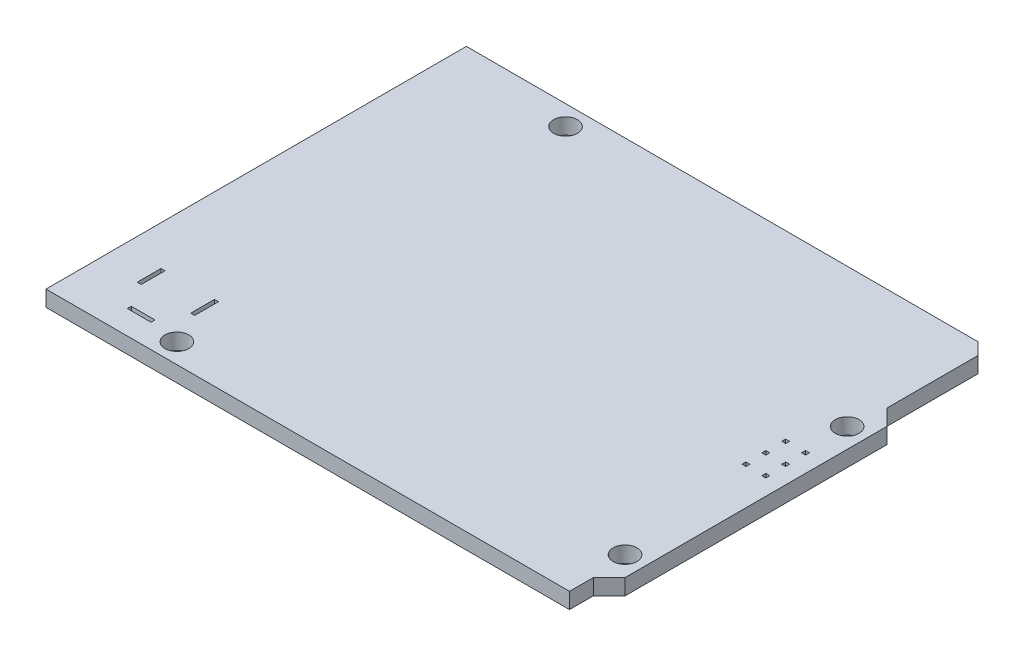
SolidWorks part; units mm, degrees
ref_plane "Front" through (0, 0, 0) normal (0, 0, 1) x (1, 0, 0)
ref_plane "Top" through (0, 0, 0) normal (0, 1, 0) x (1, 0, 0)
ref_plane "Right" through (0, 0, 0) normal (1, 0, 0) x (0, 0, -1)
sketch "Sketch1" plane through (0, 0, 0) normal (0, 1, 0) x (1, 0, 0)
  line L0 (0, 53) -> (0, 0)
  line L1 (0, 53) -> (64.5, 53)
  line L2 (64.5, 53) -> (66, 51.5)
  line L3 (66, 40) -> (68, 38)
  line L4 (68, 38) -> (68, 5)
  line L5 (66, 0) -> (66, 3)
  line L6 (66, 0) -> (0, 0)
  line L7 (66, 3) -> (68, 5)
  line L8 (66, 51.5) -> (66, 40)
  line L9 (64.5, 53) -> (66, 53) construction
  line L10 (66, 53) -> (66, 51.5) construction
  circle A0 centre (15, 50.5) radius 1.5
  circle A1 centre (14, 2.5) radius 1.5
  circle A2 centre (65.5, 7.5) radius 1.5
  circle A3 centre (65.5, 35.5) radius 1.5
  dimension "D9" = 3
  dimension "D1" = 53
  dimension "D2" = 68
  dimension "D3" = 13
  dimension "D4" = 66
  dimension "D5" = 64.5
  dimension "D6" = 15
  dimension "D7" = 3
  dimension "D8" = 5
  dimension "D10" = 15
  dimension "D11" = 2.5
  dimension "D12" = 2.5
  dimension "D13" = 17.5
  dimension "D14" = 2.5
  dimension "D15" = 7.5
  dimension "D16" = 14
extrude "Boss-Extrude1" add sketch "Sketch1" along normal blind 2
sketch "Sketch5" plane through (0, 0, 0) normal (0, -1, 0) x (1, 0, 0)
  line L0 (0, -53) -> (0, 0) construction
  line L1 (5, -6.5) -> (5.5, -6.5)
  line L2 (5, -6.5) -> (5, -9.5)
  line L3 (5, -9.5) -> (5.5, -9.5)
  line L4 (5.5, -6.5) -> (5.5, -9.5)
  line L5 (11.75, -6.5) -> (12.25, -6.5)
  line L6 (11.75, -6.5) -> (11.75, -9.5)
  line L7 (11.75, -9.5) -> (12.25, -9.5)
  line L8 (12.25, -6.5) -> (12.25, -9.5)
  line L9 (7.25, -3) -> (10.25, -3)
  line L10 (7.25, -3) -> (7.25, -3.5)
  line L11 (7.25, -3.5) -> (10.25, -3.5)
  line L12 (10.25, -3) -> (10.25, -3.5)
  line L13 (0, 0) -> (66, 0) construction
  line L14 (8.75, -3) -> (8.75, -3.5) construction
  line L15 (5, -8) -> (5.5, -8) construction
  line L16 (11.75, -8) -> (12.25, -8) construction
  dimension "D1" = 0.5
  dimension "D2" = 3
  dimension "D3" = 5
  dimension "D4" = 3
  dimension "D5" = 12.25
  dimension "D6" = 8.75
  dimension "D7" = 8
extrude "Cut-Extrude2" cut sketch "Sketch5" against normal through all
sketch "Sketch6" plane through (0, 0, 0) normal (0, -1, 0) x (-1, 0, 0)
  line L1 (-63, 24.75) -> (-63.5, 24.75)
  line L2 (-63, 24.75) -> (-63, 25.25)
  line L3 (-63, 25.25) -> (-63.5, 25.25)
  line L4 (-63.5, 24.75) -> (-63.5, 25.25)
  line L5 (-65.5, 24.75) -> (-66, 24.75)
  line L6 (-65.5, 24.75) -> (-65.5, 25.25)
  line L7 (-65.5, 25.25) -> (-66, 25.25)
  line L8 (-66, 24.75) -> (-66, 25.25)
  line L9 (-65.5, 27.25) -> (-66, 27.25)
  line L10 (-65.5, 27.25) -> (-65.5, 27.75)
  line L11 (-65.5, 27.75) -> (-66, 27.75)
  line L12 (-66, 27.25) -> (-66, 27.75)
  line L13 (-65.5, 29.75) -> (-66, 29.75)
  line L14 (-65.5, 29.75) -> (-65.5, 30.25)
  line L15 (-65.5, 30.25) -> (-66, 30.25)
  line L16 (-66, 29.75) -> (-66, 30.25)
  line L17 (-63, 29.75) -> (-63.5, 29.75)
  line L18 (-63, 29.75) -> (-63, 30.25)
  line L19 (-63, 30.25) -> (-63.5, 30.25)
  line L20 (-63.5, 29.75) -> (-63.5, 30.25)
  line L21 (-63, 27.25) -> (-63.5, 27.25)
  line L22 (-63, 27.25) -> (-63, 27.75)
  line L23 (-63, 27.75) -> (-63.5, 27.75)
  line L24 (-63.5, 27.25) -> (-63.5, 27.75)
extrude "Cut-Extrude3" cut sketch "Sketch6" against normal through all
